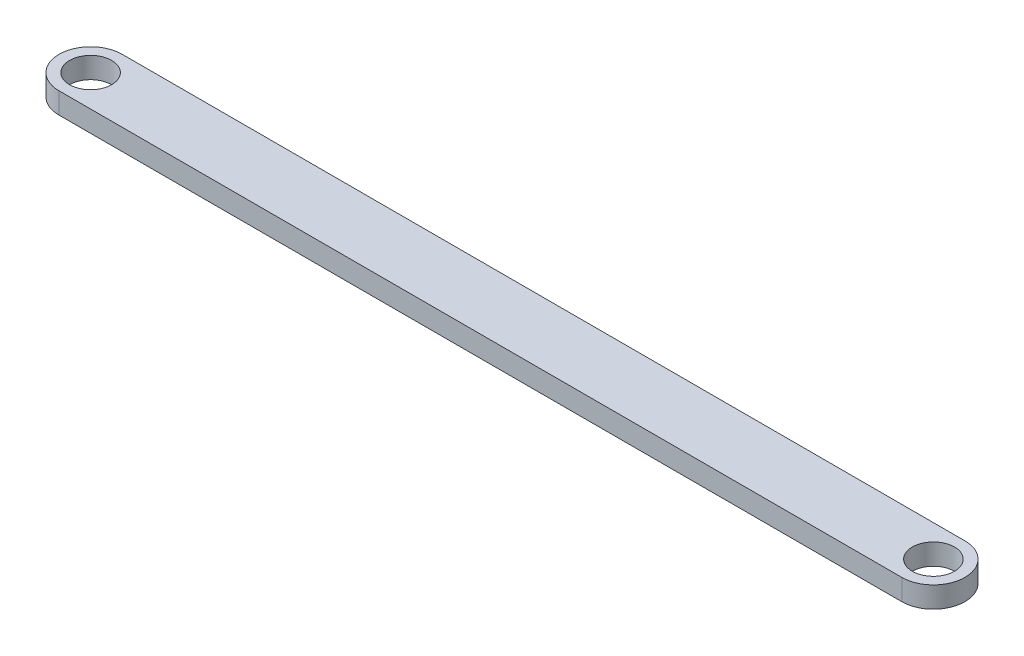
SolidWorks part; units mm, degrees
ref_plane "Front Plane" through (0, 0, 0) normal (0, 0, 1) x (1, 0, 0)
ref_plane "Top Plane" through (0, 0, 0) normal (0, 1, 0) x (1, 0, 0)
ref_plane "Right Plane" through (0, 0, 0) normal (1, 0, 0) x (0, 0, -1)
sketch "Sketch2" plane through (0, 0, 0) normal (0, 1, 0) x (1, 0, 0)
  line L0 (-208, 0) -> (192, 0) construction
  line L1 (-208, 15) -> (192, 15)
  line L2 (-208, -15) -> (192, -15)
  arc A0 (-208, 15) -> (-208, -15) centre (-208, 0) ccw
  arc A1 (192, -15) -> (192, 15) centre (192, 0) ccw
  circle A2 centre (192, 0) radius 10
  circle A3 centre (-208, 0) radius 10
  point P3 (-8, 0)
  dimension "D2" = 15
  dimension "D3" = 20
  dimension "D1" = 400
extrude "Boss-Extrude1" add sketch "Sketch2" along normal blind 10
